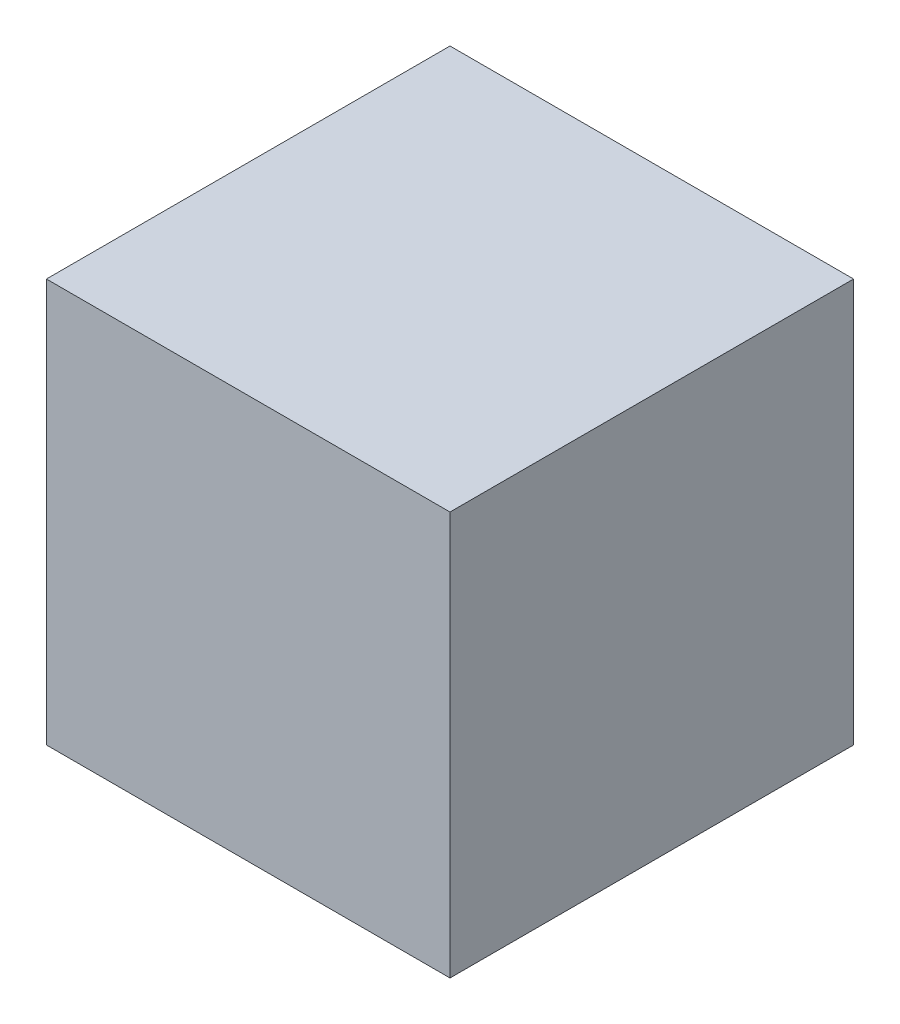
SolidWorks part; units mm, degrees
ref_plane "Front Plane" through (0, 0, 0) normal (0, 0, 1) x (1, 0, 0)
ref_plane "Top Plane" through (0, 0, 0) normal (0, 1, 0) x (1, 0, 0)
ref_plane "Right Plane" through (0, 0, 0) normal (1, 0, 0) x (0, 0, -1)
sketch "Sketch1" plane through (0, 0, 0) normal (1, 0, 0) x (0, 0, -1)
  line L1 (-311.4675, -311.4675) -> (311.4675, -311.4675)
  line L2 (-311.4675, -311.4675) -> (-311.4675, 311.4675)
  line L3 (-311.4675, 311.4675) -> (311.4675, 311.4675)
  line L4 (311.4675, -311.4675) -> (311.4675, 311.4675)
  line L5 (-311.4675, -311.4675) -> (311.4675, 311.4675) construction
  line L6 (-311.4675, 311.4675) -> (311.4675, -311.4675) construction
  point P0 (0, 0)
  dimension "Size" = 622.935
extrude "Boss-Extrude1" add sketch "Sketch1" along normal mid plane 622.935
equation "\"D1@Boss-Extrude1\" = \"Size@Sketch1\""
